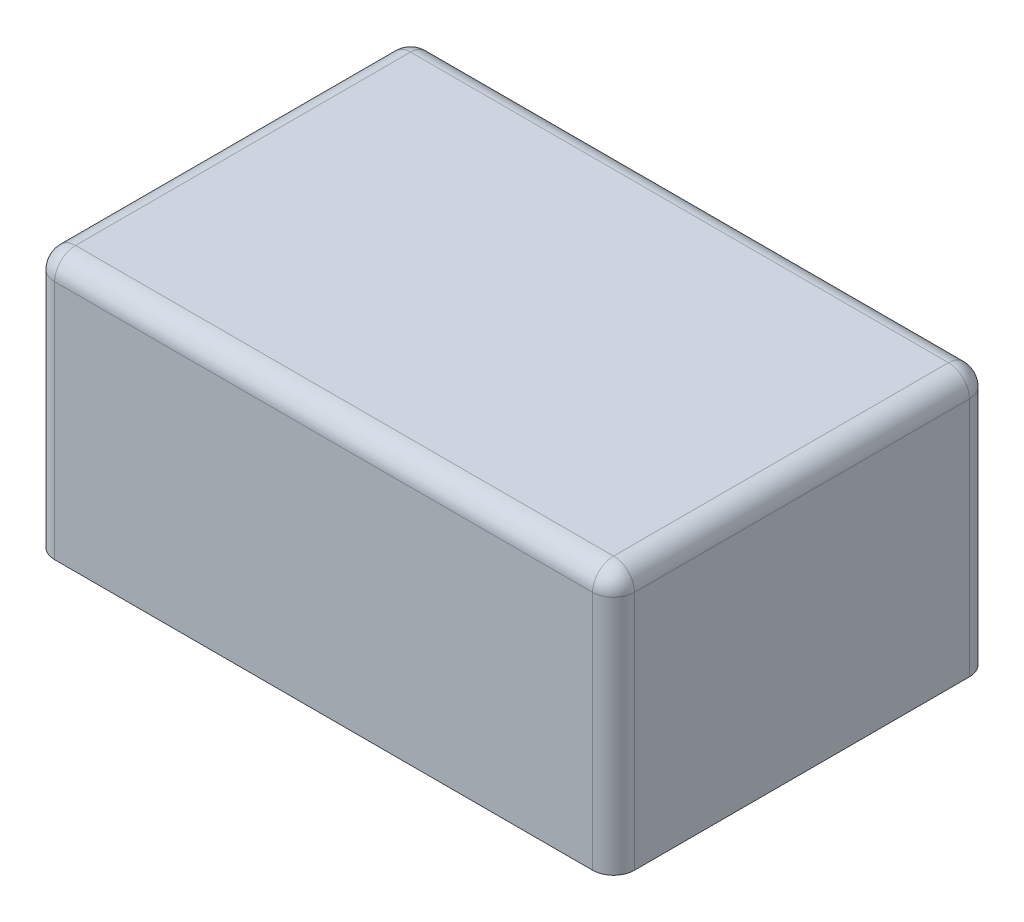
SolidWorks part; units mm, degrees
ref_plane "Front Plane" through (0, 0, 0) normal (0, 0, 1) x (1, 0, 0)
ref_plane "Top Plane" through (0, 0, 0) normal (0, 1, 0) x (1, 0, 0)
ref_plane "Right Plane" through (0, 0, 0) normal (1, 0, 0) x (0, 0, -1)
sketch "Sketch1" plane through (0, 0, 0) normal (0, 1, 0) x (1, 0, 0)
  line L1 (-27.7, -18) -> (27.7, -18)
  line L2 (-27.7, -18) -> (-27.7, 18)
  line L3 (-27.7, 18) -> (27.7, 18)
  line L4 (27.7, -18) -> (27.7, 18)
  line L5 (-27.7, -18) -> (27.7, 18) construction
  line L6 (-27.7, 18) -> (27.7, -18) construction
  point P0 (0, 0)
  dimension "D1" = 55.4
  dimension "D2" = 36
extrude "Boss-Extrude1" add sketch "Sketch1" along normal blind 25
sketch "Sketch2" plane through (0, 0, 0) normal (0, 1, 0) x (1, 0, 0)
  line L0 (-24, -6) -> (-24, 6) construction
  line L1 (24, -6) -> (24, -1) construction
  line L2 (-24, -6) -> (24, -6) construction
  circle A0 centre (-24, -6) radius 0.5
  circle A1 centre (24, -6) radius 0.5
  circle A2 centre (24, -1) radius 0.5
  circle A3 centre (-24, 6) radius 0.5
  point P4 (-24, 0)
  point P6 (0, -6)
  dimension "D4" = 1
  dimension "D1" = 48
  dimension "D2" = 12
  dimension "D3" = 5
extrude "Boss-Extrude2" add sketch "Sketch2" against normal blind 3
fillet "Fillet1" radius 2 8 edges at (27.7, 25, 0) (0, 25, -18) (-27.7, 25, 0) (0, 25, 18) (27.7, 12.5, -18) (27.7, 12.5, 18) (-27.7, 12.5, -18) (-27.7, 12.5, 18)
